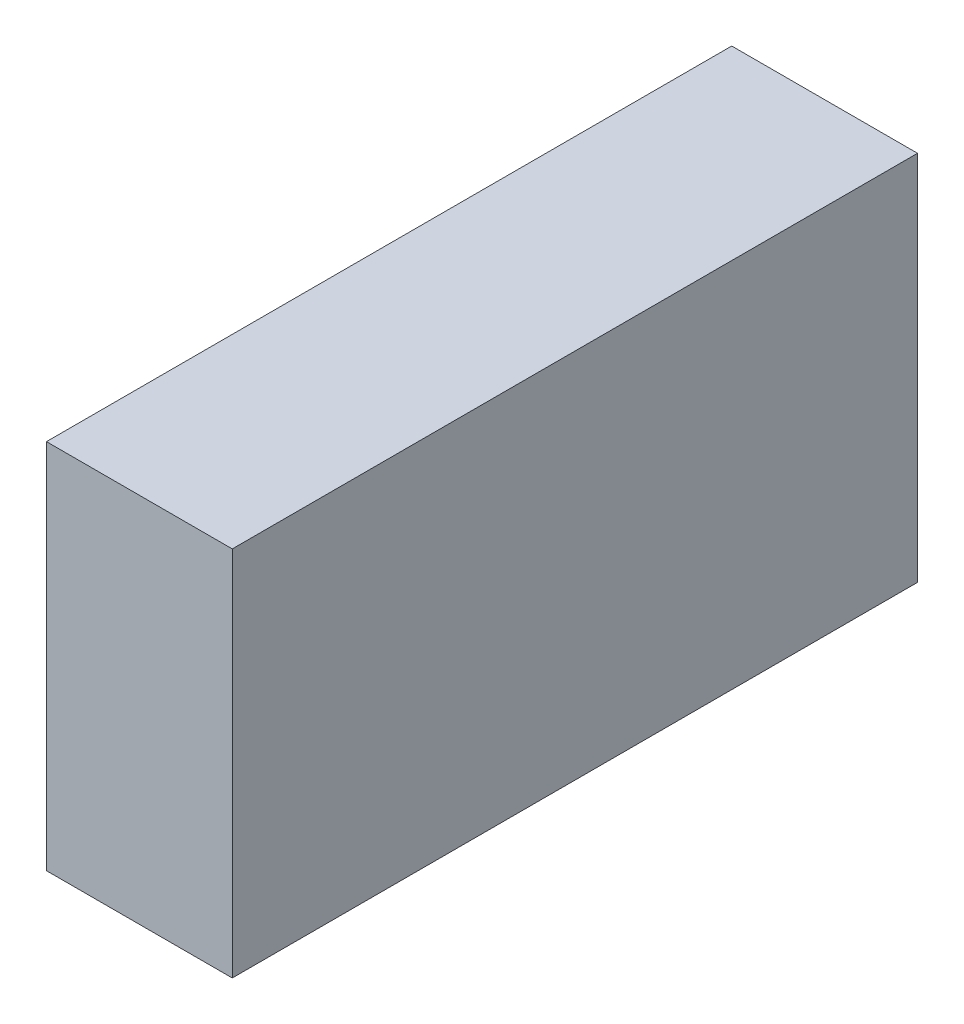
SolidWorks part; units mm, degrees
ref_plane "Front Plane" through (0, 0, 0) normal (0, 0, 1) x (1, 0, 0)
ref_plane "Top Plane" through (0, 0, 0) normal (0, 1, 0) x (1, 0, 0)
ref_plane "Right Plane" through (0, 0, 0) normal (1, 0, 0) x (0, 0, -1)
sketch "Sketch1" plane through (0, 0, 0) normal (0, 1, 0) x (1, 0, 0)
  line L1 (0, 0) -> (7.5, 0)
  line L2 (0, 0) -> (0, 27.66)
  line L3 (0, 27.66) -> (7.5, 27.66)
  line L4 (7.5, 0) -> (7.5, 27.66)
  dimension "D1" = 27.66
  dimension "D2" = 7.5
extrude "Boss-Extrude1" add sketch "Sketch1" along normal blind 25
sketch "Sketch2" plane through (0, 0, 0) normal (0, -1, 0) x (1, 0, 0)
  line L1 (0, 0) -> (7.5, 0)
  line L2 (0, 0) -> (0, -27.66)
  line L3 (0, -27.66) -> (7.5, -27.66)
  line L4 (7.5, 0) -> (7.5, -27.66)
extrude "Cut-Extrude1" cut sketch "Sketch2" against normal blind 10
